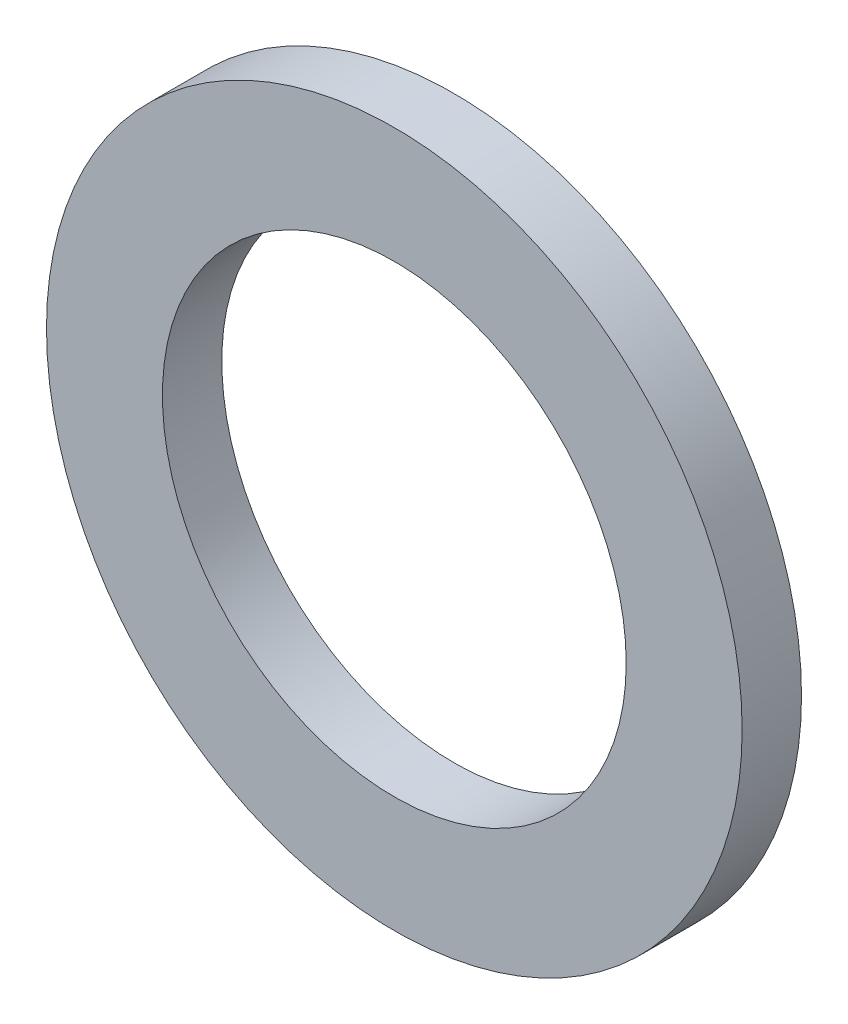
SolidWorks part; units mm, degrees
material "Chrome Stainless Steel"
ref_plane "Front Plane" through (0, 0, 0) normal (0, 0, 1) x (1, 0, 0)
ref_plane "Top Plane" through (0, 0, 0) normal (0, 1, 0) x (1, 0, 0)
ref_plane "Right Plane" through (0, 0, 0) normal (1, 0, 0) x (0, 0, -1)
sketch "Sketch1" plane through (0, 0, 0) normal (0, 0, 1) x (1, 0, 0)
  circle A0 centre (0, 0) radius 2.3813
  circle A1 centre (0, 0) radius 1.5875
  dimension "D1" = 3.175
  dimension "D2" = 4.7625
extrude "Boss-Extrude1" add sketch "Sketch1" along normal blind 0.4064
